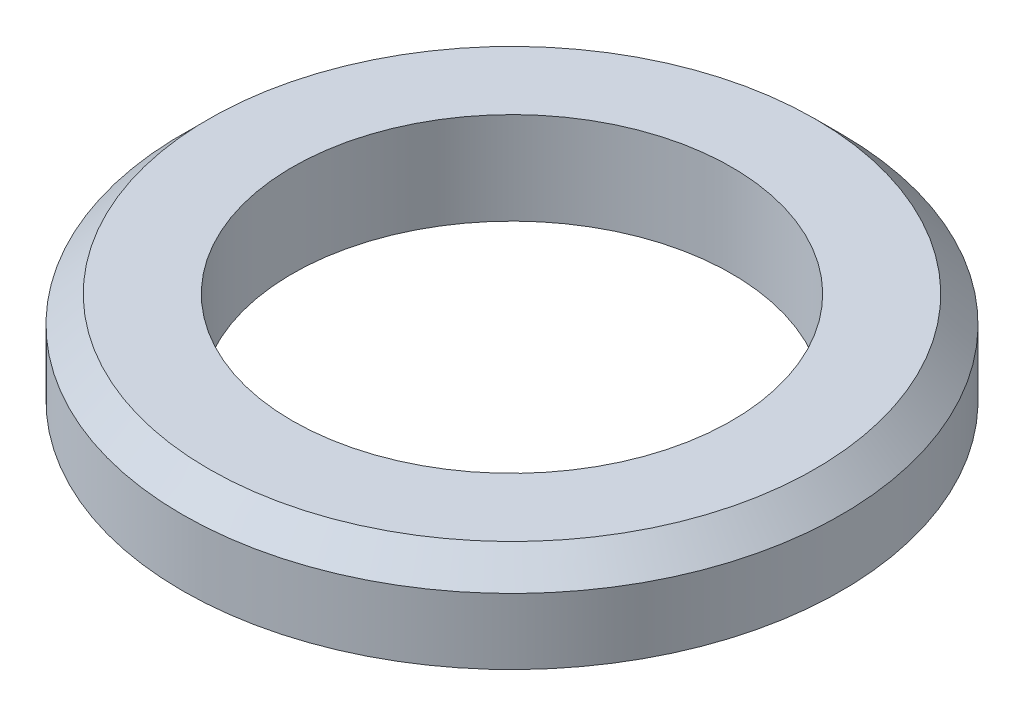
SolidWorks part; units mm, degrees
ref_plane "Alzado" through (0, 0, 0) normal (0, 0, 1) x (1, 0, 0)
ref_plane "Planta" through (0, 0, 0) normal (0, 1, 0) x (1, 0, 0)
ref_plane "Vista lateral" through (0, 0, 0) normal (1, 0, 0) x (0, 0, -1)
sketch "Sketch1" plane through (0, 0, 0) normal (0, 1, 0) x (1, 0, 0)
  circle A0 centre (0, 0) radius 0.75
  circle A1 centre (0, 0) radius 0.5
  dimension "D1" = 1.5
  dimension "D2" = 1
extrude "Boss-Extrude1" add sketch "Sketch1" along normal blind 0.21
chamfer "Chamfer1" distance 0.06 angle 45 1 edges at (0, 0.21, 0.75)
